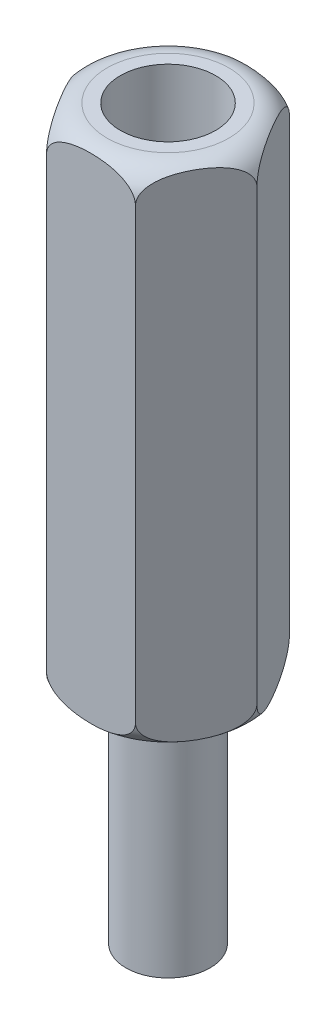
SolidWorks part; units mm, degrees
material "Brass"
ref_plane "Front Plane" through (0, 0, 0) normal (0, 0, 1) x (1, 0, 0)
ref_plane "Top Plane" through (0, 0, 0) normal (0, 1, 0) x (1, 0, 0)
ref_plane "Right Plane" through (0, 0, 0) normal (1, 0, 0) x (0, 0, -1)
sketch "Sketch1" plane through (0, 0, 0) normal (0, 1, 0) x (1, 0, 0)
  line L1 (3.1754, 0) -> (1.5877, 2.75)
  line L2 (1.5877, 2.75) -> (-1.5877, 2.75)
  line L3 (-1.5877, 2.75) -> (-3.1754, 0)
  line L4 (-3.1754, 0) -> (-1.5877, -2.75)
  line L5 (-1.5877, -2.75) -> (1.5877, -2.75)
  line L6 (1.5877, -2.75) -> (3.1754, 0)
  circle A0 centre (0, 0) radius 2.75 construction
  dimension "D1" = 5.5
extrude "Boss-Extrude1" add sketch "Sketch1" along normal blind 18
hole_wizard "M3 Clearance Hole1" positions "Sketch3" profile "Sketch2" hole size "M3" standard "ISO"
sketch "Sketch3" plane through (0, 18, 0) normal (0, 1, 0) x (-1, 0, 0)
  point P0 (0, 0)
sketch "Sketch2" plane through (0, 18, 0) normal (1, 0, 0) x (0, 0, 1)
  line L0 (0, 0) -> (0, 13.0215)
  line L1 (0, 13.0215) -> (1.7, 12)
  line L2 (1.7, 12) -> (1.7, 0)
  line L5 (1.7, 0) -> (0, 0)
  line L10 (0, 13.0215) -> (-1.7, 12) construction
  line L11 (0, -6.35) -> (0, 107.95) construction
  dimension "Hole Dia." = 3.4
  dimension "Hole Depth" = 12
  dimension "Drill Angle" = 118
sketch "Sketch4" plane through (0, 0, 0) normal (0, 0, 1) x (1, 0, 0)
  line L0 (-3.1754, 18) -> (-3.1754, 0) construction
  line L1 (-3.1754, 18) -> (-1.5877, 18) construction
  line L4 (-3.1754, 0) -> (-1.5877, 0) construction
  line L6 (-2.1754, 18) -> (-3.1754, 18)
  line L7 (-3.1754, 18) -> (-3.1754, 17)
  line L8 (-3.1754, 1) -> (-3.1754, 0)
  line L9 (-3.1754, 0) -> (-2.1754, 0)
  line L14 (0, 18) -> (0, 0) construction
  line L15 (-1.5877, 18) -> (1.5877, 18) construction
  arc A0 (-3.1754, 17) -> (-2.1754, 18) centre (-2.1754, 17) cw
  arc A2 (-3.1754, 1) -> (-2.1754, 0) centre (-2.1754, 1) ccw
  dimension "D1" = 1
revolve "Cut-Revolve1" cut sketch "Sketch4" angle 360 about L14
sketch "Sketch5" plane through (0, 0, 0) normal (0, -1, 0) x (1, 0, 0)
  circle A0 centre (0, 0) radius 1.5
  dimension "D1" = 3
extrude "Boss-Extrude2" add sketch "Sketch5" along normal blind 8
